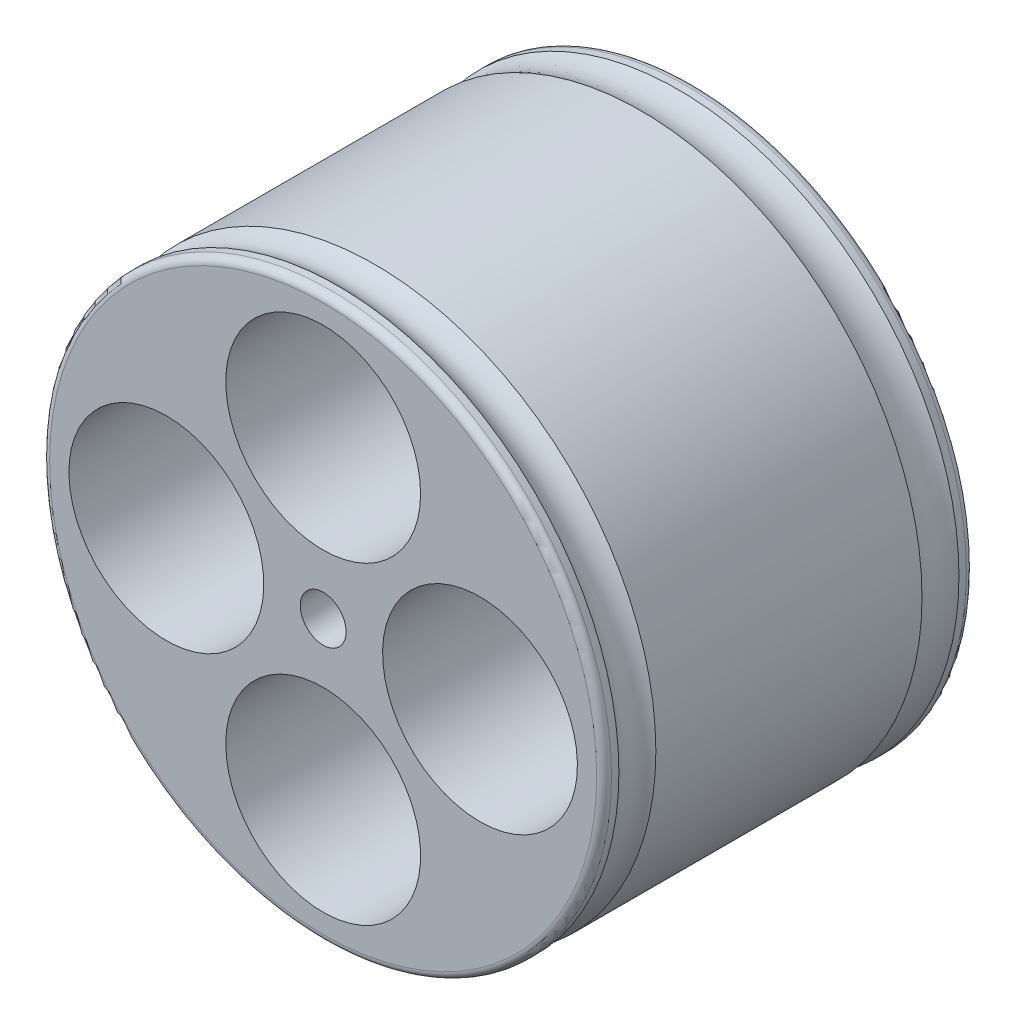
SolidWorks part; units mm, degrees
ref_plane "Front Plane" through (0, 0, 0) normal (0, 0, 1) x (1, 0, 0)
ref_plane "Top Plane" through (0, 0, 0) normal (0, 1, 0) x (1, 0, 0)
ref_plane "Right Plane" through (0, 0, 0) normal (1, 0, 0) x (0, 0, -1)
sketch "Sketch1" plane through (0, 0, 0) normal (0, 0, 1) x (1, 0, 0)
  circle A0 centre (0, 0) radius 19
  dimension "D1" = 38
extrude "Boss-Extrude1" add sketch "Sketch1" along normal blind 25
ref_axis "Axis1" through (0, 0, 8.4) along (0, 0, -1)
sketch "Sketch2" plane through (0, 0, 0) normal (1, 0, 0) x (0, 0, -1)
  line L0 (0, 19) -> (-25, 19) construction
  line L1 (-25, 19) -> (-25, -19) construction
  line L2 (0, 20.9) -> (0, -20.9) construction
  line L3 (-8.4, 0) -> (0.4, 0) construction
  line L4 (-24, 19) -> (-21.5, 19)
  line L5 (-3.5, 19) -> (-1, 19)
  arc A0 (-1, 19) -> (-3.5, 19) centre (-2.25, 21.4542) cw
  arc A1 (-21.5, 19) -> (-24, 19) centre (-22.75, 20.3125) cw
  point P12 (-22.75, 18.5)
  point P17 (-2.25, 18.7)
  dimension "D1" = 1
  dimension "D2" = 1
  dimension "D3" = 2.5
  dimension "D4" = 18.5
  dimension "D5" = 18.7
  dimension "D6" = 2.5
revolve "Cut-Revolve1" cut sketch "Sketch2" angle 360 about axis through (0, 0, 8.4) along (0, 0, -1)
fillet "Fillet1" radius 0.5 2 edges at (19, 0, 0) (19, 0, 25)
sketch "Sketch3" plane through (0, 0, 25) normal (0, 0, 1) x (1, 0, 0)
  circle A0 centre (0, 0) radius 1.55
  dimension "D1" = 3.1
extrude "Cut-Extrude1" cut sketch "Sketch3" against normal through all
sketch "Sketch4" plane through (0, 0, 25) normal (0, 0, 1) x (1, 0, 0)
  line L0 (0, -13.75) -> (0, 13.75) construction
  circle A0 centre (0, 10.6065) radius 6.589
extrude "Cut-Extrude2" cut sketch "Sketch4" against normal through all
pattern_circular "CirPattern1" count 4 over 360 about axis through (0, 0, 0) along (0, 0, 1) of "Cut-Extrude2"
